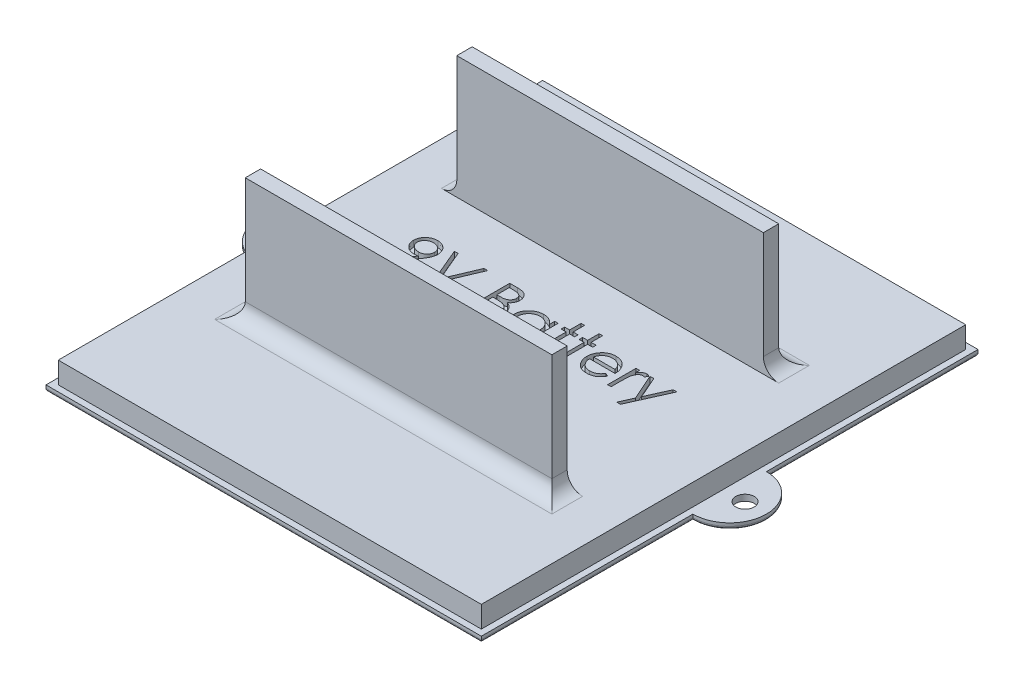
SolidWorks part; units mm, degrees
other "DetailItem2"
other "Markup1"
sketch "Sketch11" plane through (-41.5, 7, -35.5) normal (0, 1, 0) x (1, 0, 0)
sketch "Sketch12" plane through (-41.5, 7, -35.5) normal (0, 1, 0) x (1, 0, 0)
sketch "Sketch13" plane through (-41.5, 7, -35.5) normal (0, 1, 0) x (1, 0, 0)
sketch "Sketch15" plane through (-41.5, 7, -35.5) normal (0, 1, 0) x (1, 0, 0)
sketch "Sketch16" plane through (-41.5, 7, -35.5) normal (0, 1, 0) x (1, 0, 0)
sketch "Sketch17" plane through (-41.5, 7, -35.5) normal (0, 1, 0) x (1, 0, 0)
sketch "Sketch18" plane through (-41.5, 7, -35.5) normal (0, 1, 0) x (1, 0, 0)
sketch "Sketch19" plane through (-41.5, 7, -35.5) normal (0, 1, 0) x (1, 0, 0)
sketch "Sketch20" plane through (-41.5, 12, -35.5) normal (0, 1, 0) x (1, 0, 0)
sketch "Sketch21" plane through (-41.5, 25.5, -40.5) normal (0, 1, 0) x (1, 0, 0)
sketch "Sketch32" plane through (-41.5, 25.5, -40.5) normal (0, 1, 0) x (1, 0, 0)
sketch "Sketch36" plane through (-41.5, 25.5, -40.5) normal (0, 1, 0) x (1, 0, 0)
sketch "Sketch39" plane through (-41.5, 25.5, -40.5) normal (0, 1, 0) x (1, 0, 0)
sketch "Sketch42" plane through (-41.5, 25.5, -40.5) normal (0, 1, 0) x (1, 0, 0)
sketch "Sketch45" plane through (-41.5, 25.5, -35.5) normal (0, 1, 0) x (1, 0, 0)
sketch "Sketch55" plane through (-41.5, 25.5, -35.5) normal (0, 1, 0) x (1, 0, 0)
sketch "Sketch58" plane through (-41.5, 25.5, -35.5) normal (0, 1, 0) x (1, 0, 0)
other "Markup2"
sketch "Sketch37" plane through (41.5, 0.9701, -40.5) normal (1, 0, 0) x (0, 0, -1)
sketch "Sketch40" plane through (41.5, 0.9701, -40.5) normal (1, 0, 0) x (0, 0, -1)
sketch "Sketch43" plane through (41.5, 0.9701, -40.5) normal (1, 0, 0) x (0, 0, -1)
sketch "Sketch46" plane through (41.5, 0, -35.5) normal (1, 0, 0) x (0, 0, -1)
sketch "Sketch56" plane through (41.5, 0.9701, -35.5) normal (1, 0, 0) x (0, 0, -1)
sketch "Sketch59" plane through (41.5, 0.9701, -35.5) normal (1, 0, 0) x (0, 0, -1)
other "Markup3"
sketch "Sketch38" plane through (-41.5, 25.5, -40.5) normal (0, 1, 0) x (0, 0, -1)
sketch "Sketch41" plane through (-41.5, 25.5, -40.5) normal (0, 1, 0) x (0, 0, -1)
sketch "Sketch44" plane through (-41.5, 25.5, -40.5) normal (0, 1, 0) x (0, 0, -1)
sketch "Sketch47" plane through (-41.5, 25.5, -35.5) normal (0, 1, 0) x (0, 0, -1)
sketch "Sketch57" plane through (-41.5, 25.5, -35.5) normal (0, 1, 0) x (0, 0, -1)
sketch "Sketch60" plane through (-41.5, 25.5, -35.5) normal (0, 1, 0) x (0, 0, -1)
ref_plane "Front Plane" through (0, 0, 0) normal (0, 0, 1) x (1, 0, 0)
ref_plane "Top Plane" through (0, 0, 0) normal (0, 1, 0) x (1, 0, 0)
ref_plane "Right Plane" through (0, 0, 0) normal (1, 0, 0) x (0, 0, -1)
sketch "Sketch1" plane through (0, 0, 0) normal (0, 1, 0) x (1, 0, 0)
  line L1 (-35.5, -40.5) -> (35.5, -40.5)
  line L2 (-35.5, -40.5) -> (-35.5, 40.5)
  line L3 (-35.5, 40.5) -> (35.5, 40.5)
  line L4 (35.5, -40.5) -> (35.5, 40.5)
  line L5 (-35.5, -40.5) -> (35.5, 40.5) construction
  line L6 (-35.5, 40.5) -> (35.5, -40.5) construction
  point P0 (0, 0)
  dimension "D1" = 81
  dimension "D2" = 71
extrude "Boss-Extrude1" add sketch "Sketch1" along normal blind 4.5
sketch "text" plane through (0, 4.5, 0) normal (0, 1, 0) x (1, 0, 0)
  line L0 (-35.4043, 1.8177) -> (35.5957, 1.8177) construction
  text T0 "9V Battery \r\nHolder" font "Century Gothic" height in points 24
extrude "Cut-Extrude1" cut sketch "text" against normal blind 1
sketch "Sketch4" plane through (0, 4.5, 0) normal (0, 1, 0) x (1, 0, 0)
  line L0 (-35.5, 40.5) -> (-35.5, -40.5) construction
  line L1 (-35.5, 6) -> (-35.5, -6)
  arc A0 (-35.5, 6) -> (-35.5, -6) centre (-35.5, 0) ccw
  dimension "D1" = 6
extrude "Boss-Extrude3" add sketch "Sketch4" against normal up to surface (4.5 mm away) up to face at (0, 0, 0)
sketch "Sketch5" plane through (0, 4.5, 0) normal (0, 1, 0) x (1, 0, 0)
  line L0 (-35.5, 40.5) -> (-35.5, 6) construction
  circle A0 centre (-38, 0) radius 1.5
  dimension "D1" = 3
  dimension "D2" = 2.5
extrude "Cut-Extrude2" cut sketch "Sketch5" against normal up to surface (4.5 mm away) up to face at (-12.8333, 0, 0)
mirror "Mirror3" about plane through (0, 0, 0) normal (1, 0, 0) of "Boss-Extrude3", "Cut-Extrude2"
sketch "Sketch61" plane through (0, 4.5, 0) normal (0, 1, 0) x (1, 0, 0)
  line L0 (35.5, 6) -> (35.5, 40.5) construction
  line L1 (-34.5, -39.5) -> (34.5, -39.5)
  line L2 (-34.5, -39.5) -> (-34.5, 39.5)
  line L3 (-34.5, 39.5) -> (34.5, 39.5)
  line L4 (34.5, -39.5) -> (34.5, 39.5)
  line L5 (-34.5, -39.5) -> (34.5, 39.5) construction
  line L6 (-34.5, 39.5) -> (34.5, -39.5) construction
  line L7 (35.5, 40.5) -> (-35.5, 40.5) construction
  line L8 (-44.5, 49.5) -> (44.5, 49.5)
  line L9 (44.5, -49.5) -> (44.5, 49.5)
  line L10 (-44.5, -49.5) -> (44.5, -49.5)
  line L11 (-44.5, -49.5) -> (-44.5, 49.5)
  point P0 (0, 0)
  dimension "D1" = 1
  dimension "D2" = 1
  dimension "D3" = 10
extrude "Cut-Extrude21" cut sketch "Sketch61" against normal offset from surface (3.5 mm away) 1 up to face at (38, 0, -1.5)
sketch "Sketch9" plane through (0, 4.5, 0) normal (0, 1, 0) x (1, 0, 0)
  line L1 (-25, 18.5) -> (25, 18.5)
  line L2 (-25, 18.5) -> (-25, 16)
  line L3 (-25, 16) -> (25, 16)
  line L4 (25, 18.5) -> (25, 16)
  point P4 (0, 16)
  dimension "D1" = 50
  dimension "D2" = 2.5
  dimension "D3" = 16
extrude "top track" add sketch "Sketch9" along normal blind 20 contours L2 L1 L4 L3
fillet "Fillet1" radius 2.5 3 edges at (-25, 4.5, -17.25) (0, 4.5, -18.5) (25, 4.5, -17.25)
mirror "Mirror4" about plane through (0, 0, 0) normal (0, 0, 1) of "top track", "Fillet1"
fillet "Fillet2" radius 0.5 8 edges at (35.5, 0, 23.25) (41.5, 0, 0) (35.5, 0, -23.25) (0, 0, -40.5) (-35.5, 0, -23.25) (-41.5, 0, 0) (-35.5, 0, 23.25) (0, 0, 40.5)
equation "\"Screw_Diameter\"=3"
